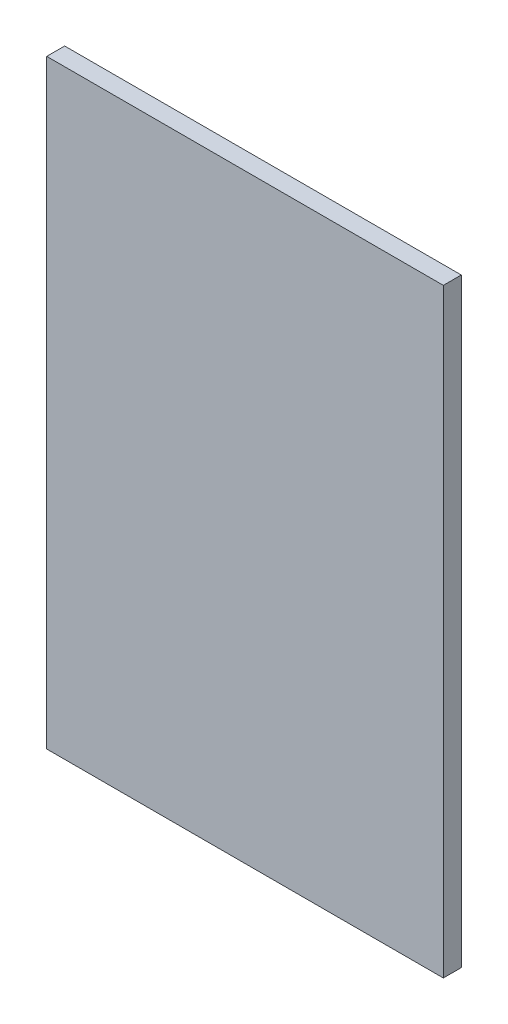
SolidWorks part; units mm, degrees
ref_plane "Front Plane" through (0, 0, 0) normal (0, 0, 1) x (1, 0, 0)
ref_plane "Top Plane" through (0, 0, 0) normal (0, 1, 0) x (1, 0, 0)
ref_plane "Right Plane" through (0, 0, 0) normal (1, 0, 0) x (0, 0, -1)
sketch "Sketch1" plane through (0, 0, 0) normal (0, 0, 1) x (1, 0, 0)
  line L1 (199, -301) -> (-199, -301)
  line L2 (199, -301) -> (199, 301)
  line L3 (199, 301) -> (-199, 301)
  line L4 (-199, -301) -> (-199, 301)
  line L5 (199, -301) -> (-199, 301) construction
  line L6 (199, 301) -> (-199, -301) construction
  point P0 (0, 0)
  dimension "D1" = 602
  dimension "D2" = 398
extrude "Boss-Extrude1" add sketch "Sketch1" along normal blind 18
equation "\"H_DSP\"=18"
equation "\"D1@Boss-Extrude1\"=\"H_DSP\""
